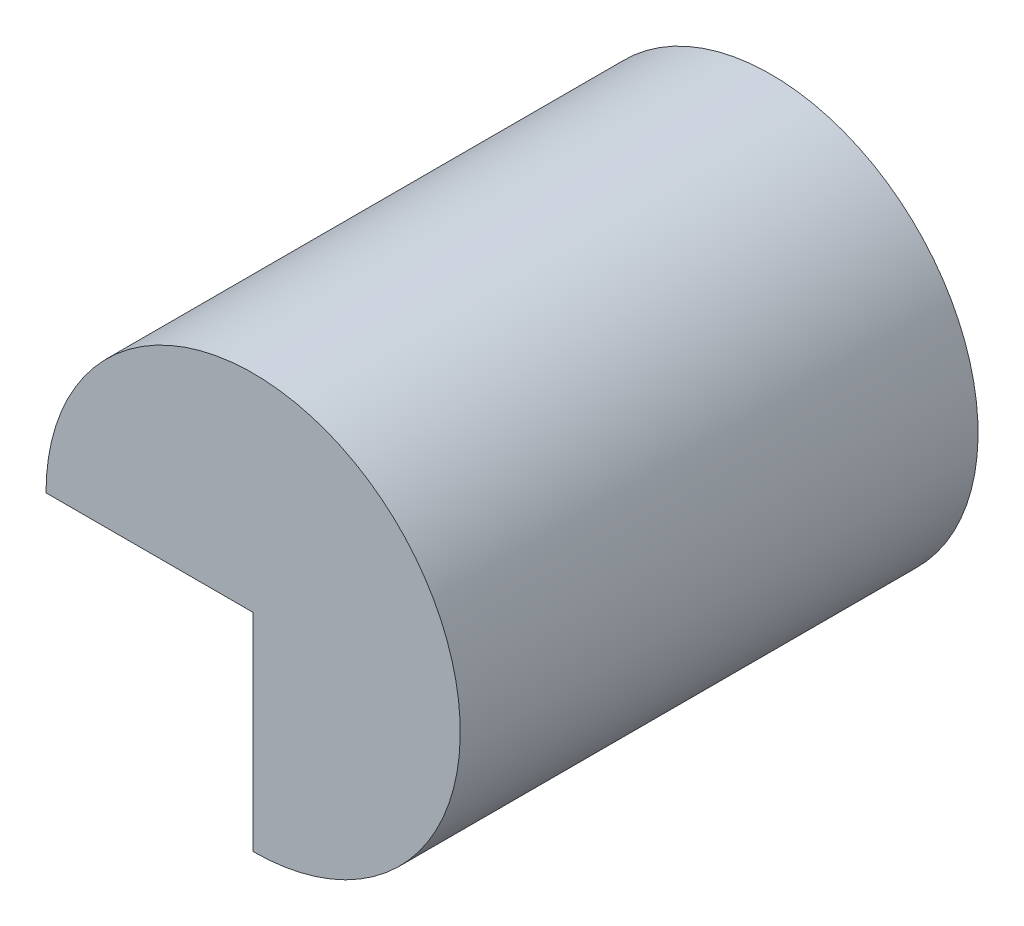
SolidWorks part; units mm, degrees
ref_plane "Front Plane" through (0, 0, 0) normal (0, 0, 1) x (1, 0, 0)
ref_plane "Top Plane" through (0, 0, 0) normal (0, 1, 0) x (1, 0, 0)
ref_plane "Right Plane" through (0, 0, 0) normal (1, 0, 0) x (0, 0, -1)
sketch "Sketch1" plane through (0, 0, 0) normal (0, 0, 1) x (1, 0, 0)
  line L0 (-10, 0) -> (0, 0)
  line L1 (0, 0) -> (0, -10)
  arc A0 (0, -10) -> (-10, 0) centre (0, 0) ccw
  dimension "D3" = 10
  dimension "D1" = 10
  dimension "D2" = 10
extrude "Boss-Extrude1" add sketch "Sketch1" along normal blind 25
